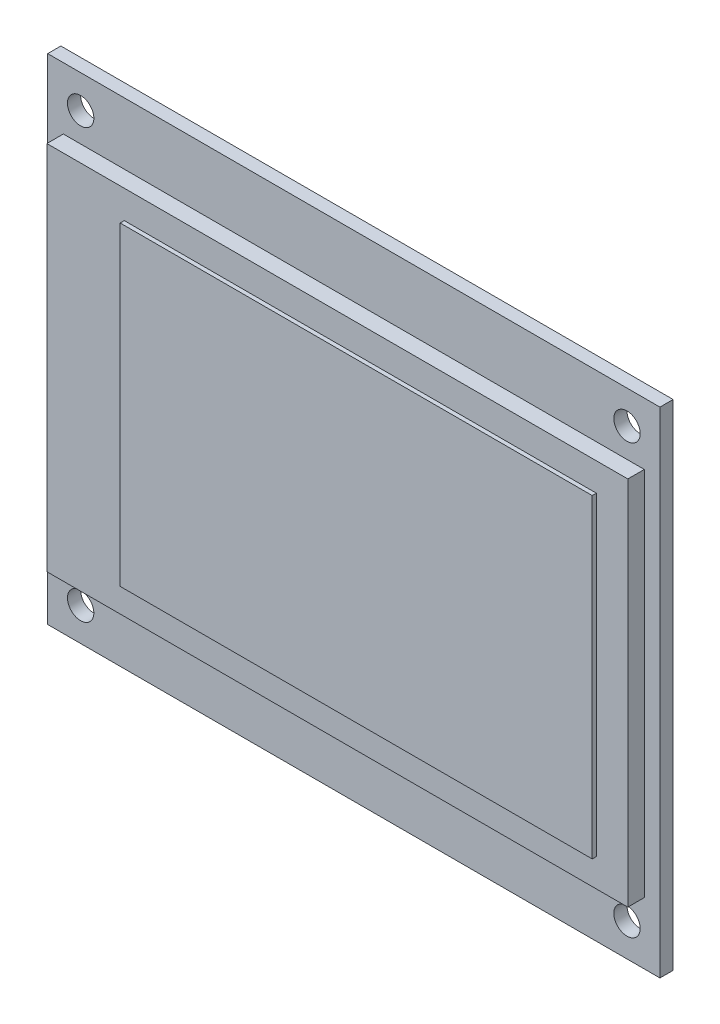
SolidWorks part; units mm, degrees
material "Ceramic Porcelain"
ref_plane "Front Plane" through (0, 0, 0) normal (0, 0, 1) x (1, 0, 0)
ref_plane "Top Plane" through (0, 0, 0) normal (0, 1, 0) x (1, 0, 0)
ref_plane "Right Plane" through (0, 0, 0) normal (1, 0, 0) x (0, 0, -1)
sketch "Sketch1" plane through (0, 0, 0) normal (0, 0, 1) x (1, 0, 0)
  line L1 (0, 0) -> (74.3, 0)
  line L2 (0, 0) -> (0, 60)
  line L3 (0, 60) -> (74.3, 60)
  line L4 (74.3, 0) -> (74.3, 60)
  dimension "D1" = 74.3
  dimension "D2" = 60
extrude "Boss-Extrude1" add sketch "Sketch1" along normal blind 1.6
sketch "Sketch2" plane through (0, 0, 1.6) normal (0, 0, 1) x (1, 0, 0)
  line L0 (0, 0) -> (74.3, 0) construction
  line L1 (1.9, 22.5) -> (0, 22.5)
  line L2 (1.9, 22.5) -> (1.9, 7.5)
  line L3 (1.9, 7.5) -> (0, 7.5)
  line L4 (0, 22.5) -> (0, 7.5)
  line L5 (0, 60) -> (0, 0) construction
  dimension "D1" = 7.5
  dimension "D2" = 1.9
  dimension "D3" = 15
extrude "Cut-Extrude1" cut sketch "Sketch2" against normal through all
hole_wizard "Ø3.2 (3.2) Diameter Hole1" positions "Sketch4" profile "Sketch3" hole size "Ø3.2" standard "ANSI Metric"
sketch "Sketch4" plane through (0, 0, 1.6) normal (0, 0, 1) x (1, 0, 0)
  point P0 (4, 56)
  point P2 (70.3, 56)
  point P4 (70.3, 4)
  point P6 (4, 4)
  dimension "D1" = 66.3
  dimension "D2" = 52
  dimension "D3" = 4
  dimension "D4" = 4
sketch "Sketch3" plane through (4, 56, 1.6) normal (1, 0, 0) x (0, -1, 0)
  line L0 (0, 0) -> (0, 60.9614)
  line L1 (0, 60.9614) -> (1.6, 60)
  line L2 (1.6, 60) -> (1.6, 0)
  line L5 (1.6, 0) -> (0, 0)
  line L10 (0, 60.9614) -> (-1.6, 60) construction
  line L11 (0, -6.35) -> (0, 107.95) construction
  dimension "Hole Dia." = 3.2
  dimension "Hole Depth" = 60
  dimension "Drill Angle" = 118
sketch "Sketch6" plane through (0, 0, 1.6) normal (0, 0, 1) x (1, 0, 0)
  line L0 (74.3, 0) -> (74.3, 60) construction
  line L1 (1.9, 52.5) -> (72.4, 52.5)
  line L2 (1.9, 52.5) -> (1.9, 7.5)
  line L3 (1.9, 7.5) -> (72.4, 7.5)
  line L4 (72.4, 52.5) -> (72.4, 7.5)
  line L5 (0, 60) -> (0, 22.5) construction
  line L6 (74.3, 60) -> (0, 60) construction
  line L7 (0, 0) -> (74.3, 0) construction
  dimension "D1" = 1.9
  dimension "D2" = 1.9
  dimension "D3" = 7.5
  dimension "D4" = 7.5
extrude "Boss-Extrude2" add sketch "Sketch6" along normal blind 2
sketch "Sketch7" plane through (0, 0, 3.6) normal (0, 0, 1) x (1, 0, 0)
  line L0 (72.4, 7.5) -> (72.4, 52.5) construction
  line L1 (11.292, 49.096) -> (68.58, 49.096)
  line L2 (11.292, 49.096) -> (11.292, 10.904)
  line L3 (11.292, 10.904) -> (68.58, 10.904)
  line L4 (68.58, 49.096) -> (68.58, 10.904)
  line L5 (1.9, 30) -> (72.4, 30) construction
  line L6 (1.9, 52.5) -> (1.9, 7.5) construction
  dimension "D1" = 57.288
  dimension "D2" = 38.192
  dimension "D3" = 3.82
  dimension "D4" = 19.096
extrude "Boss-Extrude3" add sketch "Sketch7" along normal blind 0.5
